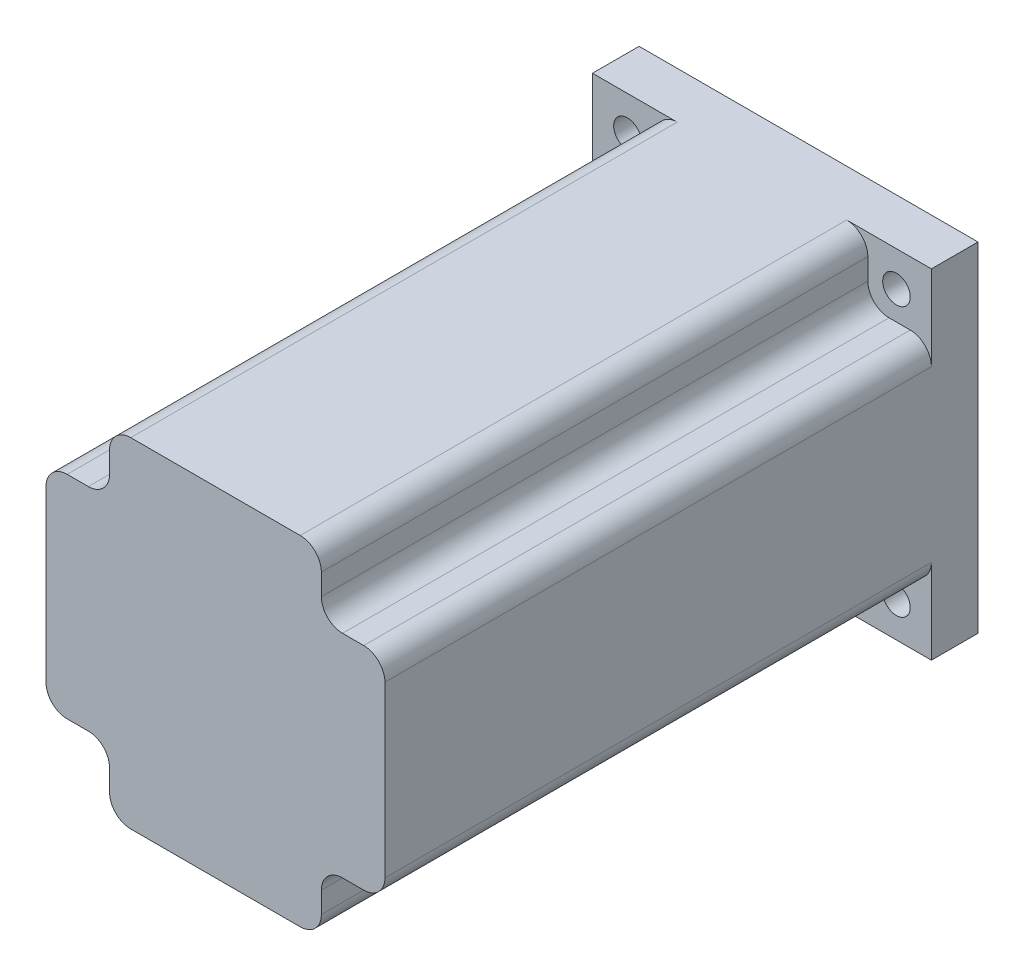
SolidWorks part; units mm, degrees
material "A3钢"
ref_plane "前视基准面" through (0, 0, 0) normal (0, 0, 1) x (1, 0, 0)
ref_plane "上视基准面" through (0, 0, 0) normal (0, 1, 0) x (1, 0, 0)
ref_plane "右视基准面" through (0, 0, 0) normal (1, 0, 0) x (0, 0, -1)
sketch "草图1" plane through (0, 0, 0) normal (0, 0, 1) x (1, 0, 0)
  line L1 (-40, -40) -> (40, -40)
  line L2 (-40, -40) -> (-40, 40)
  line L3 (-40, 40) -> (40, 40)
  line L4 (40, -40) -> (40, 40)
  line L5 (-40, -40) -> (40, 40) construction
  line L6 (-40, 40) -> (40, -40) construction
  point P0 (0, 0)
  dimension "D1" = 80
  dimension "D2" = 80
extrude "凸台-拉伸1" add sketch "草图1" along normal blind 140
sketch "草图2" plane through (0, 0, 140) normal (0, 0, 1) x (1, 0, 0)
  line L0 (-72.2391, 0) -> (88.8371, 0) construction
  line L1 (0, 109.7062) -> (0, -80.373) construction
  line L2 (30, 25) -> (35, 25)
  line L3 (-30, 25) -> (-35, 25)
  line L4 (40, -40) -> (40, 40)
  line L5 (40, 40) -> (-40, 40)
  line L6 (-40, 40) -> (-40, -40)
  line L7 (-40, -40) -> (40, -40)
  line L8 (40, -20) -> (40, 20)
  line L9 (20, 40) -> (-20, 40)
  line L10 (-40, 20) -> (-40, -20)
  line L11 (-20, -40) -> (20, -40)
  line L12 (-25, 30) -> (-25, 35)
  line L13 (25, 30) -> (25, 35)
  line L14 (25, -30) -> (25, -35)
  line L15 (-25, 25) -> (-40, 40) construction
  line L16 (-25, 40) -> (-40, 25) construction
  line L17 (30, -25) -> (35, -25)
  line L18 (-25, -30) -> (-25, -35)
  line L19 (-30, -25) -> (-35, -25)
  arc A0 (-35, 25) -> (-40, 20) centre (-35, 20) ccw
  arc A1 (-25, 35) -> (-20, 40) centre (-20, 35) cw
  arc A2 (-30, 25) -> (-25, 30) centre (-30, 30) ccw
  arc A3 (-25, -35) -> (-20, -40) centre (-20, -35) ccw
  arc A4 (-35, -25) -> (-40, -20) centre (-35, -20) cw
  arc A5 (-25, -30) -> (-30, -25) centre (-30, -30) ccw
  arc A6 (25, -35) -> (20, -40) centre (20, -35) cw
  arc A7 (25, -30) -> (30, -25) centre (30, -30) cw
  arc A8 (35, -25) -> (40, -20) centre (35, -20) ccw
  arc A9 (35, 25) -> (40, 20) centre (35, 20) cw
  arc A10 (30, 25) -> (25, 30) centre (30, 30) cw
  arc A11 (25, 35) -> (20, 40) centre (20, 35) ccw
  point P9 (-32.5, 32.5)
  point P33 (-25, -40)
  point P36 (-40, -25)
  point P39 (-25, -25)
  point P42 (25, -40)
  point P45 (25, -25)
  point P48 (40, -25)
  point P51 (40, 25)
  point P54 (25, 25)
  point P57 (25, 40)
  dimension "D3" = 5
  dimension "D4" = 5
  dimension "D2" = 15
  dimension "D1" = 0
extrude "切除-拉伸1" cut sketch "草图2" against normal blind 129 flip side to cut
sketch "草图3" plane through (0, 0, 11) normal (0, 0, 1) x (1, 0, 0)
  line L1 (-31.75, -31.75) -> (31.75, -31.75)
  line L2 (-31.75, -31.75) -> (-31.75, 31.75)
  line L3 (-31.75, 31.75) -> (31.75, 31.75)
  line L4 (31.75, -31.75) -> (31.75, 31.75)
  line L5 (-31.75, -31.75) -> (31.75, 31.75) construction
  line L6 (-31.75, 31.75) -> (31.75, -31.75) construction
  point P0 (0, 0)
  dimension "D1" = 63.5
hole_wizard "Ø6.5 (6.5) 直径孔1" positions "3D草图1" profile "草图5" hole size "Ø6.5" standard "GB" end condition through all
sketch3d "3D草图1"
  point P0 (-31.75, 31.75, 11)
  point P3 (31.75, 31.75, 11)
  point P6 (31.75, -31.75, 11)
  point P8 (-31.75, -31.75, 11)
  point P11 (31.75, -31.75, 11)
  point P13 (-31.75, -31.75, 11)
sketch "草图5" plane through (-31.75, 31.75, 11) normal (1, 0, 0) x (0, -1, 0)
  line L0 (0, 0) -> (0, 11)
  line L1 (0, 11) -> (3.25, 11)
  line L2 (3.25, 11) -> (3.25, 0)
  line L5 (3.25, 0) -> (0, 0)
  line L11 (0, -6.35) -> (0, 107.95) construction
  dimension "通孔孔直径" = 6.5
  dimension "通孔孔深度" = 11
